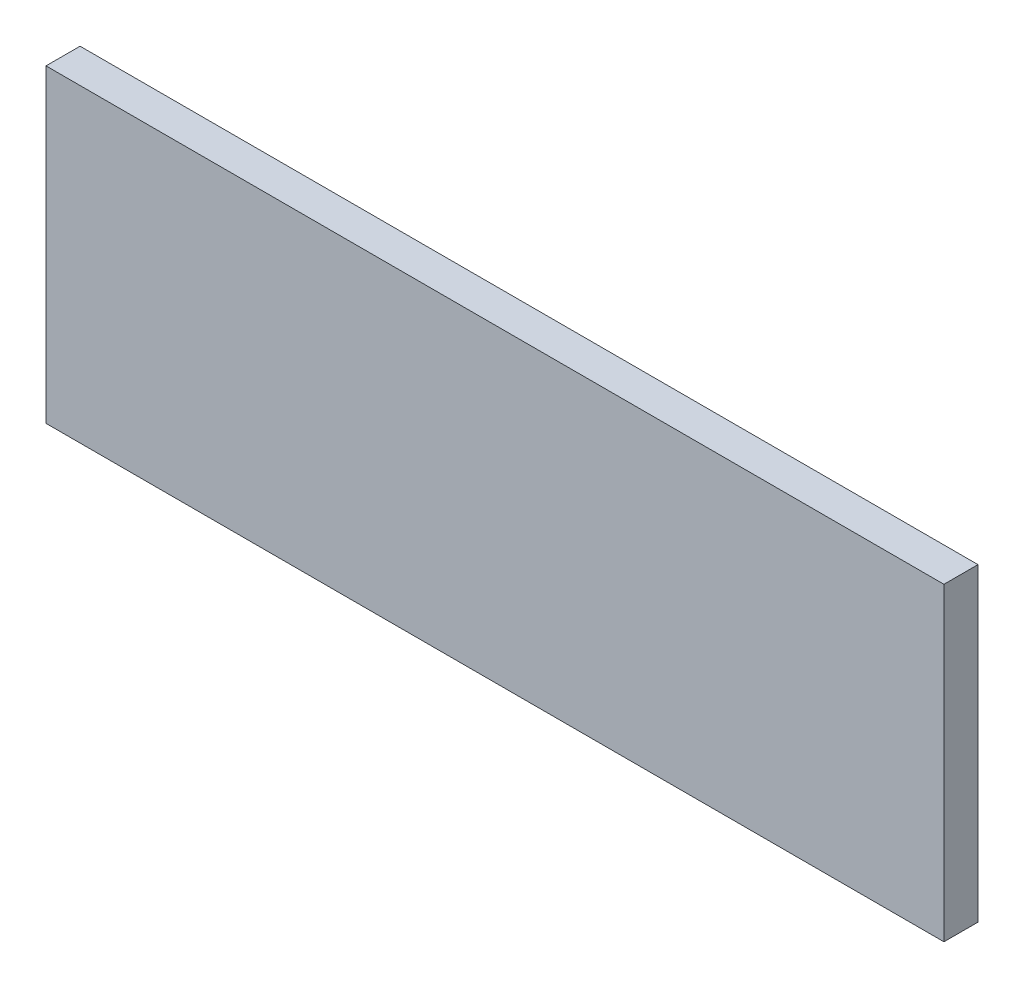
SolidWorks part; units mm, degrees
ref_plane "Ebene vorne" through (0, 0, 0) normal (0, 0, 1) x (1, 0, 0)
ref_plane "Ebene oben" through (0, 0, 0) normal (0, 1, 0) x (1, 0, 0)
ref_plane "Ebene rechts" through (0, 0, 0) normal (1, 0, 0) x (0, 0, -1)
sketch "Sketch1" plane through (0, 0, 0) normal (0, 0, 1) x (1, 0, 0)
  line L1 (-290, -100) -> (290, -100)
  line L2 (-290, -100) -> (-290, 100)
  line L3 (-290, 100) -> (290, 100)
  line L4 (290, -100) -> (290, 100)
  line L5 (-290, -100) -> (290, 100) construction
  line L6 (-290, 100) -> (290, -100) construction
  point P0 (0, 0)
  dimension "D1" = 580
  dimension "D2" = 200
extrude "Boss-Extrude1" add sketch "Sketch1" along normal blind 22
